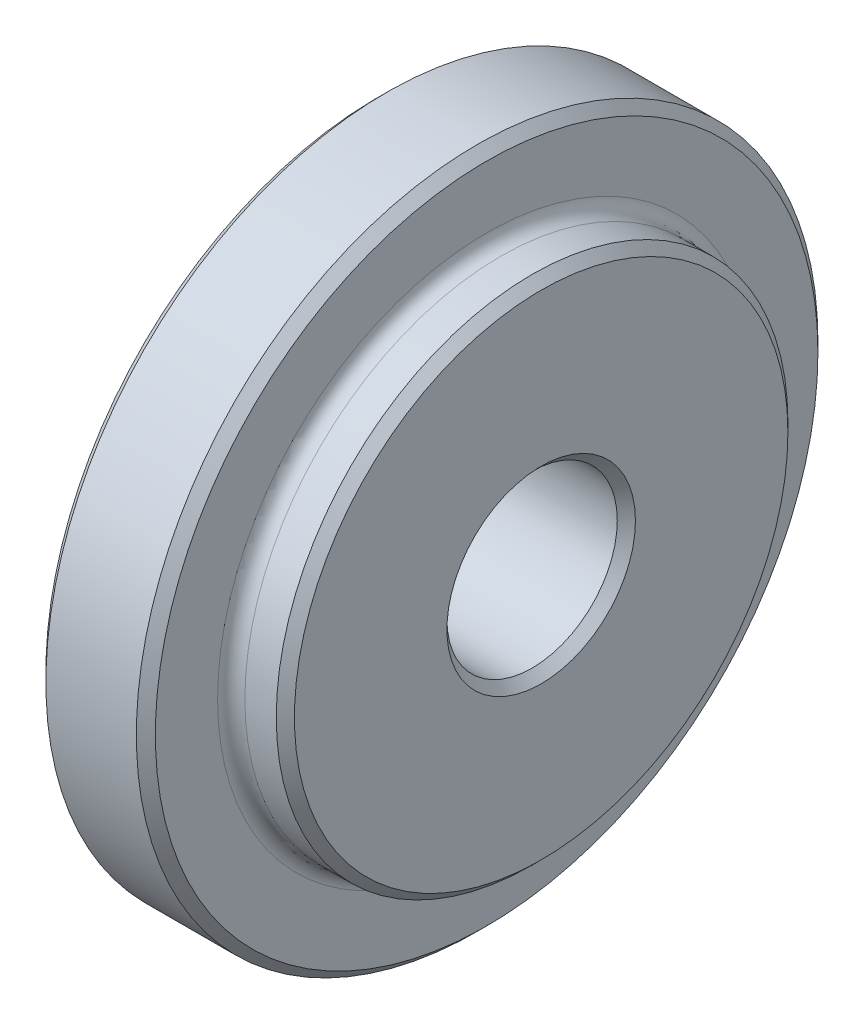
SolidWorks part; units mm, degrees
material "PE High Density"
ref_plane "Front Plane" through (0, 0, 0) normal (0, 0, 1) x (1, 0, 0)
ref_plane "Top Plane" through (0, 0, 0) normal (0, 1, 0) x (1, 0, 0)
ref_plane "Right Plane" through (0, 0, 0) normal (1, 0, 0) x (0, 0, -1)
sketch "Sketch2" plane through (0, 0, 0) normal (0, 0, 1) x (1, 0, 0)
  line L0 (27.554, 50.3007) -> (27.554, 36.5593)
  line L2 (39.746, 50.3515) -> (39.746, 36.572)
  line L3 (36.1666, 55.6093) -> (31.11, 55.6093)
  line L4 (30.602, 55.1013) -> (30.602, 51.6215)
  line L5 (36.698, 55.0779) -> (36.698, 51.5981)
  line L6 (28.062, 50.8341) -> (29.8146, 50.8341)
  line L10 (37.4832, 50.8595) -> (39.238, 50.8595)
  line L12 (27.554, 50.3007) -> (28.062, 50.8341)
  line L13 (30.602, 55.1013) -> (31.11, 55.6093)
  line L14 (36.1666, 55.6093) -> (36.698, 55.0779)
  line L15 (39.238, 50.8595) -> (39.746, 50.3515)
  line L21 (33.6383, 36.5593) -> (27.554, 36.5593)
  line L22 (33.6383, 36.5593) -> (39.746, 36.572)
  arc A2 (29.8146, 50.8341) -> (30.602, 51.6215) centre (29.8146, 51.6215) ccw
  arc A3 (36.698, 51.5981) -> (37.4832, 50.8595) centre (37.4839, 51.6469) ccw
  dimension "D3" = 12.192
  dimension "D4" = 6.096
revolve "Revolve1" add sketch "Sketch2" angle 360 about L21
sketch "Sketch3" plane through (27.554, 0, 0) normal (-1, 0, 0) x (0, 0, 1)
  circle A0 centre (0, 36.5593) radius 4.7625
extrude "Cut-Extrude1" cut sketch "Sketch3" against normal through all
chamfer "Chamfer1" distance 0.508 angle 45 2 edges at (39.746, 36.5593, 4.7625) (27.554, 36.5593, 4.7625)
